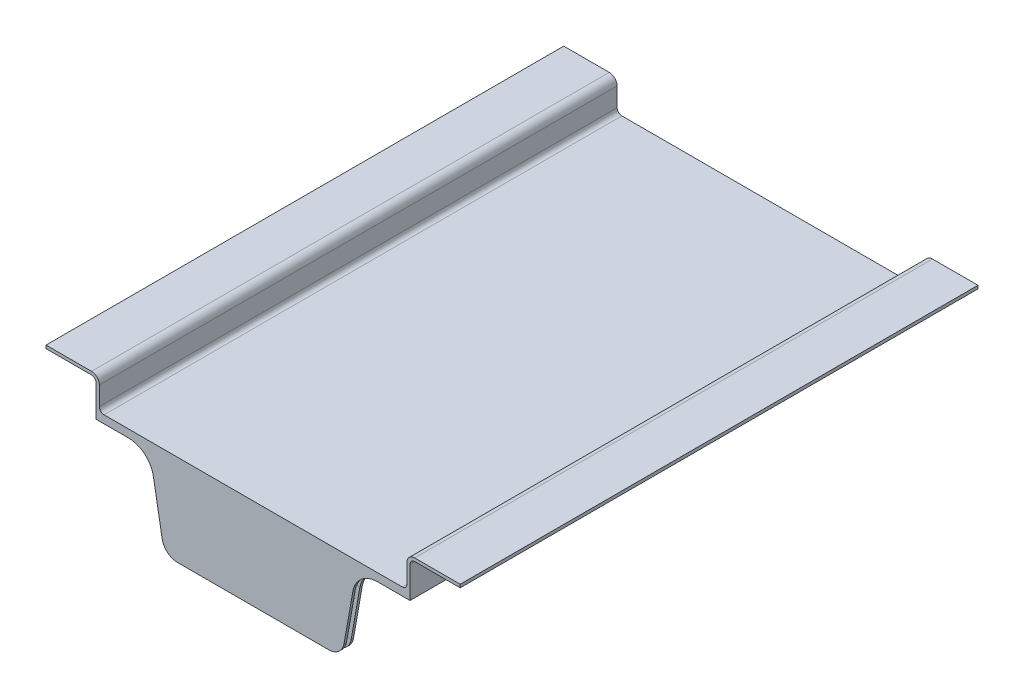
SolidWorks part; units mm, degrees
ref_plane "Plan de face" through (0, 0, 0) normal (0, 0, 1) x (1, 0, 0)
ref_plane "Plan de dessus" through (0, 0, 0) normal (0, 1, 0) x (1, 0, 0)
ref_plane "Plan de droite" through (0, 0, 0) normal (1, 0, 0) x (0, 0, -1)
sketch "Esquisse1" plane through (0, 0, 0) normal (0, 0, 1) x (1, 0, 0)
  line L3 (-95, 2) -> (95, 2)
  line L5 (103, 22) -> (127, 22)
  line L7 (103, 20) -> (127, 20)
  line L10 (100, 0) -> (-100, 0)
  line L11 (-127, 22) -> (-103, 22)
  line L12 (-127, 20) -> (-103, 20)
  line L18 (127, 20) -> (132, 20)
  line L20 (127, 22) -> (132, 22)
  line L21 (132, 20) -> (132, 22)
  line L22 (-127, 20) -> (-132, 20)
  line L24 (-127, 22) -> (-132, 22)
  line L25 (-132, 20) -> (-132, 22)
  line L26 (100, 17) -> (100, 0)
  line L27 (98, 5) -> (98, 17)
  line L28 (-100, 17) -> (-100, 0)
  line L29 (-98, 5) -> (-98, 17)
  arc A23 (98, 17) -> (103, 22) centre (103, 17) cw
  arc A24 (-103, 22) -> (-98, 17) centre (-103, 17) cw
  arc A25 (-103, 20) -> (-100, 17) centre (-103, 17) cw
  arc A26 (103, 20) -> (100, 17) centre (103, 17) ccw
  arc A27 (-98, 5) -> (-95, 2) centre (-95, 5) ccw
  arc A28 (98, 5) -> (95, 2) centre (95, 5) cw
  point P10 (103, 22)
  point P24 (103, 22)
  point P32 (132, 22)
  point P33 (127, 20)
  point P34 (0, 0)
  dimension "D9" = 3
  dimension "D10" = 5
  dimension "D11" = 200
  dimension "D12" = 264
  dimension "D7" = 3
  dimension "D6" = 5
  dimension "D3" = 2
  dimension "D4" = 2
  dimension "D5" = 2
  dimension "D8" = 2
  dimension "D19" = 2
  dimension "D20" = 2
  dimension "D22" = 20
  dimension "D23" = 20
  dimension "D24" = 5
  dimension "D25" = 5
extrude "Boss.-Extru.1" add sketch "Esquisse1" along normal blind 320 and the other way blind 10
sketch "Esquisse3" plane through (0, 0, 0) normal (0, -1, 0) x (-1, 0, 0)
  line L0 (0, -314) -> (0, 0) construction
  line L3 (-100, -314) -> (100, -314)
  line L4 (100, -320) -> (100, -314)
  line L5 (132, 10) -> (132, -320) construction
  line L6 (100, -320) -> (-100, -320) construction
  line L7 (100, -320) -> (-100, -320)
  line L12 (-100, -314) -> (-100, -320)
  dimension "D1" = 6
  dimension "D3" = 32
extrude "Boss.-Extru.2" add sketch "Esquisse3" along normal blind 56.1
sketch "Esquisse41" plane through (0, 0, 0) normal (0, -1, 0) x (1, 0, 0)
  line L0 (-100, -10) -> (-100, 314) construction
  line L5 (95, 320) -> (-95, 320) construction
  line L14 (-100, 314) -> (100, 314) construction
  line L15 (84, 314) -> (-84, 314)
  line L16 (94, 304) -> (94, 6)
  line L17 (84, -4) -> (-84, -4)
  line L18 (-94, 304) -> (-94, 6)
  line L19 (-100, -10) -> (100, -10) construction
  line L20 (100, -10) -> (100, 320) construction
  line L21 (-100, -10) -> (-100, 314) construction
  line L23 (100, -10) -> (-100, -10)
  line L24 (100, -10) -> (100, 320)
  line L25 (100, 320) -> (-100, 320)
  line L26 (-100, -10) -> (-100, 320)
  arc A4 (-94, 6) -> (-84, -4) centre (-84, 6) ccw
  arc A5 (94, 6) -> (84, -4) centre (84, 6) cw
  arc A6 (84, 314) -> (94, 304) centre (84, 304) cw
  arc A7 (-84, 314) -> (-94, 304) centre (-84, 304) ccw
  point P28 (94, 314)
  dimension "D2" = 6
  dimension "D4" = 10
  dimension "D5" = 10
  dimension "D1" = 6
  dimension "D3" = 6
extrude "Boss.-Extru.9" add sketch "Esquisse41" along normal blind 3
sketch "Esquisse24" plane through (0, 0, 320) normal (0, 0, 1) x (1, 0, 0)
  line L0 (65.8862, -3) -> (56.5233, -56.1)
  line L1 (-100, -56.1) -> (100, -56.1) construction
  line L2 (-65.8862, -3) -> (-56.5233, -56.1)
  line L10 (100, -3) -> (100, -56.1)
  line L13 (100, -3) -> (65.8862, -3)
  line L14 (100, -56.1) -> (-100, -56.1) construction
  line L20 (100, -56.1) -> (56.5233, -56.1)
  line L22 (-56.5233, -56.1) -> (-100, -56.1)
  line L23 (-65.8862, -3) -> (-100, -3)
  line L24 (-100, -3) -> (-100, -56.1)
  point P4 (0, 0)
  point P5 (0, 0)
  point P7 (0, 0)
  point P15 (65.8862, -3)
  dimension "D4" = 34.1138
  dimension "D6" = 100
extrude "Enlèv. mat.-Extru.22" cut sketch "Esquisse24" against normal blind 6
fillet "Congé8" radius 10 2 edges at (-56.5233, -56.1, 317) (56.5233, -56.1, 317)
fillet "Congé9" radius 16 2 edges at (-65.8862, -3, 317) (65.8862, -3, 317)
sketch3d "Esquisse3D2"
  line L0 (0, -3, -7) -> (84, -3, -7)
  line L1 (97, -3, 6) -> (97, -3, 304)
  line L2 (0, -3, -4) -> (0, -3, -10) construction
  line L3 (-84, -3, -4) -> (84, -3, -4) construction
  line L4 (-100, -3, -10) -> (100, -3, -10) construction
  line L5 (84, -3, 304) -> (84, -3, 317) construction
  line L6 (84, -3, 317) -> (79.3118, -3, 317)
  line L10 (0, -56.1, 317) -> (48.1323, -56.1, 317)
  line L11 (57.9804, -47.8365, 317) -> (63.5549, -16.2216, 317)
  line L12 (0, -56.1, 314) -> (0, -56.1, 320) construction
  line L13 (-48.1323, -56.1, 314) -> (48.1323, -56.1, 314) construction
  line L14 (48.1323, -56.1, 320) -> (-48.1323, -56.1, 320) construction
  arc A0 (97, -3, 304) -> (84, -3, 317) centre (84, -3, 304) ccw
  arc A1 (84, -3, -4) -> (94, -3, 6) centre (84, -3, 6) ccw construction
  arc A2 (84, -3, -7) -> (97, -3, 6) centre (84, -3, 6) ccw
  arc A3 (94, -3, 304) -> (84, -3, 314) centre (84, -3, 304) ccw construction
  arc A4 (48.1323, -56.1, 317) -> (57.9804, -47.8365, 317) centre (48.1323, -46.1, 317) ccw
  arc A5 (63.5549, -16.2216, 317) -> (79.3118, -3, 317) centre (79.3118, -19, 317) ccw
  point P4 (84, -16, 304)
  point P16 (84, -13, 6)
  point P22 (84, -13, 304)
  point P23 (0, 0, 0)
  point P26 (97, -3, -7)
  point P27 (84, -16, 6)
  point P33 (56.5233, -56.1, 317)
  point P34 (48.1323, -46.1, 327)
  point P42 (65.8862, -3, 317)
  point P43 (79.3118, -19, 301)
  point P49 (48.1323, -46.1, 299.7819)
  point P50 (0, 0, 0)
  point P51 (36.2865, -56.1, 317)
  dimension "D1" = 10
  dimension "D2" = 16
sketch "Esquisse48" plane through (0, 0, 0) normal (1, 0, 0) x (0, 0, -1)
  line L1 (8.5, -3) -> (5.5, -3)
  line L2 (8.5, -3) -> (8.5, -0.6)
  line L3 (8.5, -0.6) -> (5.5, -0.6)
  line L4 (5.5, -3) -> (5.5, -0.6)
  dimension "D1" = 3
  dimension "D2" = 2.4
sweep "Enlèvement de matière-Balayage2" cut profiles "Esquisse48" path "Esquisse3D2"
